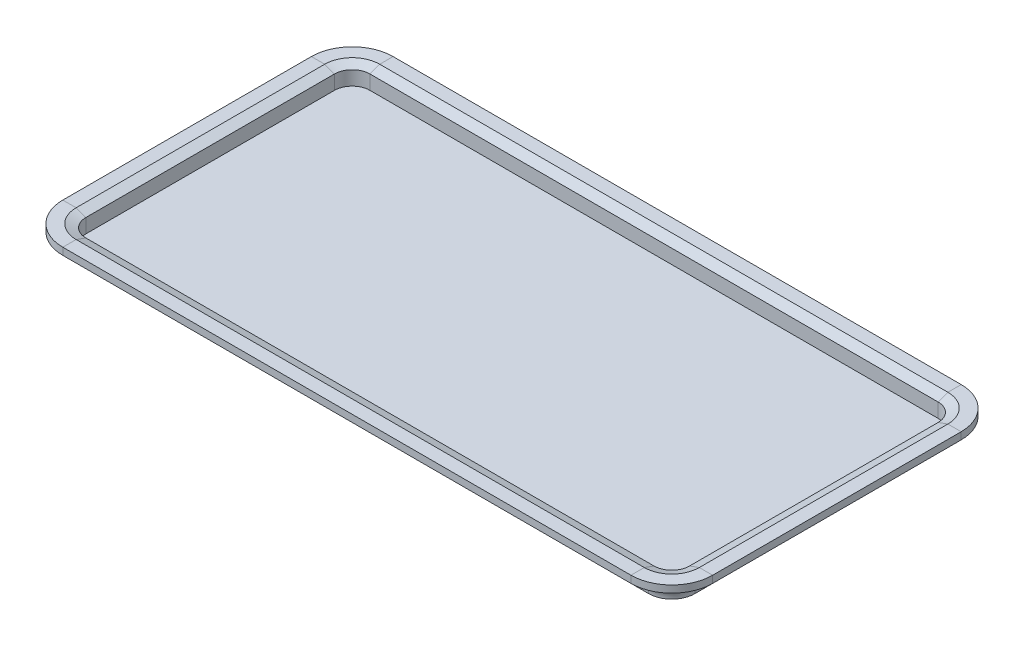
SolidWorks part; units mm, degrees
ref_plane "前视基准面" through (0, 0, 0) normal (0, 0, 1) x (1, 0, 0)
ref_plane "上视基准面" through (0, 0, 0) normal (0, 1, 0) x (1, 0, 0)
ref_plane "右视基准面" through (0, 0, 0) normal (1, 0, 0) x (0, 0, -1)
sketch "草图1" plane through (0, 0, 0) normal (0, 1, 0) x (1, 0, 0)
  line L0 (-1064.3162, 0) -> (1126.0684, 0) construction
  line L1 (0, 695.6197) -> (0, -688.3547) construction
  line L3 (-800, 400) -> (800, 400)
  line L4 (-850, 350) -> (-850, -350)
  line L5 (-800, -400) -> (800, -400)
  line L6 (850, 350) -> (850, -350)
  arc A0 (800, 400) -> (850, 350) centre (800, 350) cw
  arc A1 (800, -400) -> (850, -350) centre (800, -350) ccw
  arc A2 (-800, 400) -> (-850, 350) centre (-800, 350) ccw
  arc A3 (-850, -350) -> (-800, -400) centre (-800, -350) ccw
  point P11 (850, 400)
  point P16 (-850, 400)
  point P19 (-850, -400)
  dimension "D3" = 50
  dimension "D1" = 1700
  dimension "D2" = 800
extrude "凸台-拉伸1" add sketch "草图1" along normal blind 20
ref_plane "基准面1" through (0, 0, 350) normal (0, 0, 1) x (0, -1, 0)
sketch "草图3" plane through (0, 0, 350) normal (0, 0, 1) x (0, -1, 0)
  line L0 (0, 850) -> (-60, 850)
  line L1 (-60, 850) -> (-70, 877.4748)
  line L2 (-70, 877.4748) -> (-70, 915)
  line L3 (-70, 915) -> (-50, 915)
  line L4 (0, 850) -> (0, 865)
  line L5 (-20, 850) -> (-20, 800) construction
  arc A0 (-50, 915) -> (0, 865) centre (0, 915) ccw
  dimension "D1" = 15
  dimension "D2" = 20
  dimension "D3" = 110
  dimension "D4" = 40
  dimension "D5" = 10
sketch "草图4" plane through (0, 20, 0) normal (0, 1, 0) x (1, 0, 0)
  line L4 (800, 400) -> (-800, 400)
  line L5 (-850, 350) -> (-850, -350)
  line L6 (-800, -400) -> (800, -400)
  line L7 (850, -350) -> (850, 350)
  line L8 (800, 400) -> (-800, 400)
  line L9 (-850, 350) -> (-850, -350)
  line L10 (-800, -400) -> (800, -400)
  line L11 (850, -350) -> (850, 350)
  arc A4 (850, 350) -> (800, 400) centre (800, 350) ccw
  arc A5 (-800, 400) -> (-850, 350) centre (-800, 350) ccw
  arc A6 (-850, -350) -> (-800, -400) centre (-800, -350) ccw
  arc A7 (800, -400) -> (850, -350) centre (800, -350) ccw
  arc A8 (850, 350) -> (800, 400) centre (800, 350) ccw
  arc A9 (-800, 400) -> (-850, 350) centre (-800, 350) ccw
  arc A10 (-850, -350) -> (-800, -400) centre (-800, -350) ccw
  arc A11 (800, -400) -> (850, -350) centre (800, -350) ccw
  dimension "D1" = 0
sweep "扫描1" add profiles "草图3" path "草图4"
